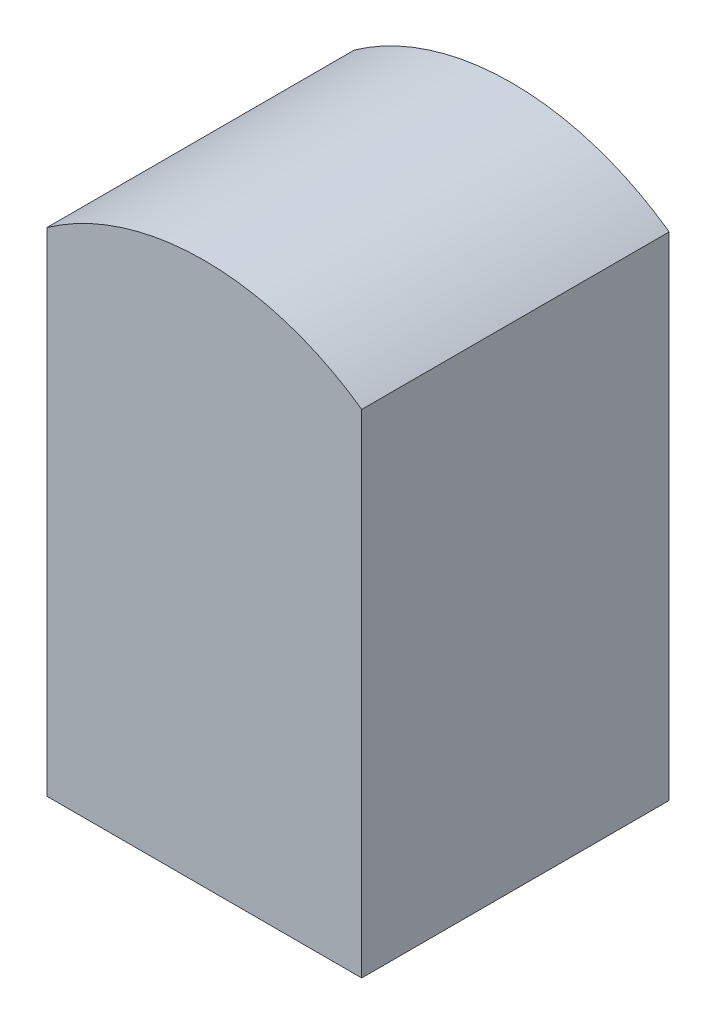
SolidWorks part; units mm, degrees
ref_plane "前视基准面" through (0, 0, 0) normal (0, 0, 1) x (1, 0, 0)
ref_plane "上视基准面" through (0, 0, 0) normal (0, 1, 0) x (1, 0, 0)
ref_plane "右视基准面" through (0, 0, 0) normal (1, 0, 0) x (0, 0, -1)
sketch "草图1" plane through (0, 0, 0) normal (0, 0, 1) x (1, 0, 0)
  line L1 (-42.5, 73.25) -> (42.5, 73.25)
  line L2 (-42.5, 73.25) -> (-42.5, -73.25)
  line L3 (-42.5, -73.25) -> (42.5, -73.25)
  line L4 (42.5, 73.25) -> (42.5, -73.25)
  line L5 (-42.5, 73.25) -> (42.5, -73.25) construction
  line L6 (-42.5, -73.25) -> (42.5, 73.25) construction
  circle A0 centre (0, 0) radius 73.25
  point P0 (0, 0)
  dimension "D1" = 85
  dimension "D2" = 146.5
extrude "凸台-拉伸1" add sketch "草图1" along normal blind 83 contours L4 A0 L2 | A0 L3 L4 | A0 L2 L3
